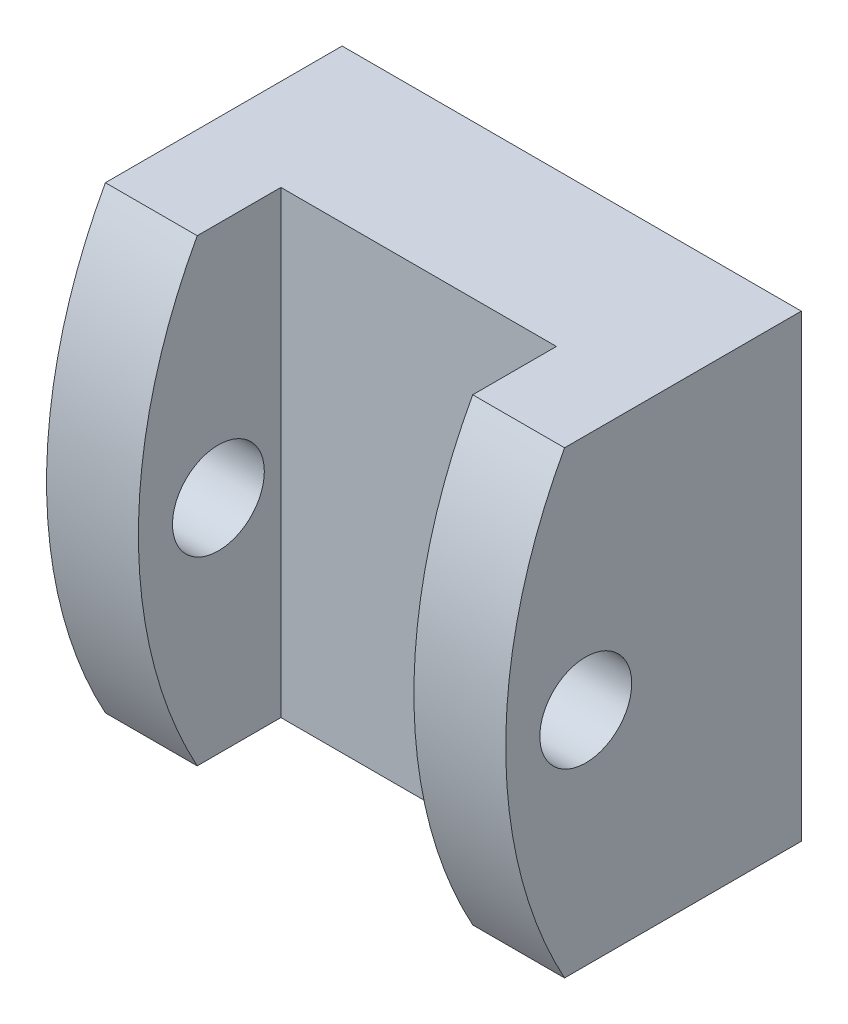
SolidWorks part; units mm, degrees
ref_plane "Front Plane" through (0, 0, 0) normal (0, 0, 1) x (1, 0, 0)
ref_plane "Top Plane" through (0, 0, 0) normal (0, 1, 0) x (1, 0, 0)
ref_plane "Right Plane" through (0, 0, 0) normal (1, 0, 0) x (0, 0, -1)
sketch "Sketch1" plane through (0, 0, 0) normal (0, 0, 1) x (1, 0, 0)
  line L1 (0, 0) -> (-15, 0)
  line L2 (0, 0) -> (0, -15)
  line L3 (0, -15) -> (-15, -15)
  line L4 (-15, 0) -> (-15, -15)
  dimension "D1" = 15
  dimension "D2" = 15
extrude "Boss-Extrude1" add sketch "Sketch1" along normal blind 5
sketch "Sketch2" plane through (0, 0, 5) normal (0, 0, 1) x (1, 0, 0)
  line L0 (0, 0) -> (-15, 0) construction
  line L1 (-3, 0) -> (0, 0)
  line L2 (-3, 0) -> (-3, -15)
  line L3 (-3, -15) -> (0, -15)
  line L4 (0, 0) -> (0, -15)
  line L5 (-15, -15) -> (0, -15) construction
  line L6 (0, -15) -> (0, 0) construction
  line L7 (-7.5, 0) -> (-7.5, -15) construction
  line L8 (-15, 0) -> (-12, 0)
  line L9 (-15, 0) -> (-15, -15)
  line L10 (-15, -15) -> (-12, -15)
  line L11 (-12, 0) -> (-12, -15)
  dimension "D1" = 3
  dimension "D2" = 3
extrude "Boss-Extrude2" add sketch "Sketch2" along normal blind 5
sketch "Sketch3" plane through (0, 0, 0) normal (1, 0, 0) x (0, 0, -1)
  line L0 (-10, 0) -> (-7.4945, 0)
  line L2 (-10, 0) -> (-10, -15)
  line L3 (-10, 0) -> (0, 0) construction
  line L4 (-7.4945, 0) -> (-7.4945, -15)
  line L5 (-10, -15) -> (0, -15) construction
  line L6 (-7.4945, -15) -> (-10, -15)
  arc A0 (-7.7337, 0) -> (-7.7337, -15) centre (5.9451, -7.5) ccw
  line M8 (-10, 0) -> (-10, -15)
  line M9 (-10, -15) -> (0, -15)
extrude "Cut-Extrude1" cut sketch "Sketch3" against normal blind 18 contours A0 L0 M8 M9
sketch "Sketch4" plane through (-12, 0, 0) normal (1, 0, 0) x (0, 0, -1)
  circle A0 centre (-7.0414, -7.7625) radius 1.5
  dimension "D1" = 3
extrude "Cut-Extrude2" cut sketch "Sketch4" against normal through all both and the other way through all
